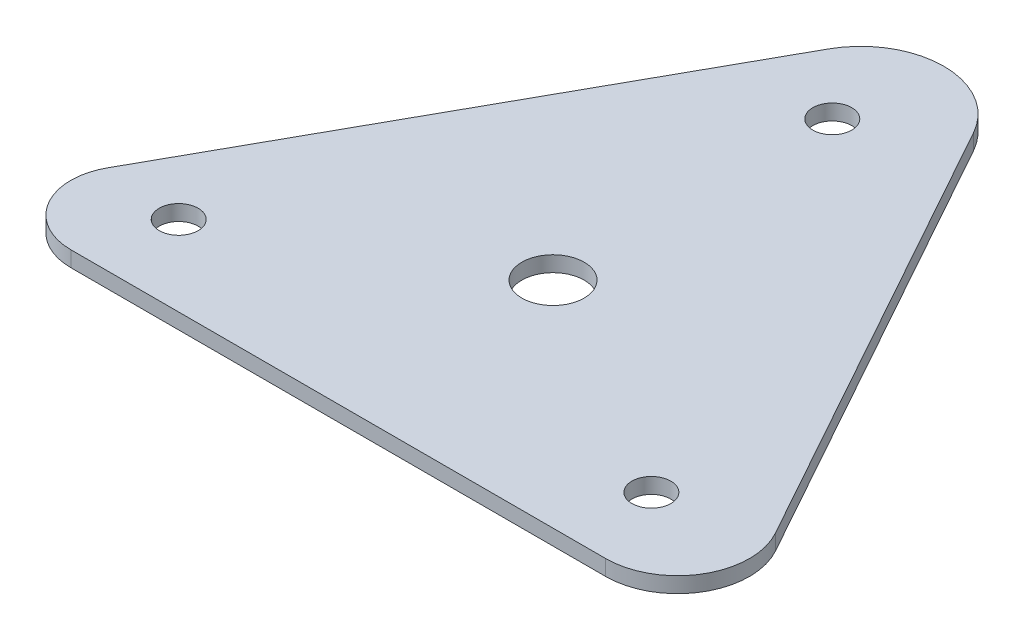
SolidWorks part; units mm, degrees
ref_plane "Front Plane" through (0, 0, 0) normal (0, 0, 1) x (1, 0, 0)
ref_plane "Top Plane" through (0, 0, 0) normal (0, 1, 0) x (1, 0, 0)
ref_plane "Right Plane" through (0, 0, 0) normal (1, 0, 0) x (0, 0, -1)
sketch "Sketch1" plane through (0, 0, 0) normal (0, 1, 0) x (1, 0, 0)
  line L0 (0, 0) -> (109.1184, 0)
  line L1 (121.9408, 21.7924) -> (71.4013, 112.7596)
  line L2 (41.8181, 112.7596) -> (-10.7131, 18.2075)
  line L3 (5.6585, 16.358) -> (54.5592, 100.7792) construction
  line L4 (54.5592, 100.7792) -> (102.0769, 16.358) construction
  line L5 (5.6585, 16.358) -> (102.0769, 16.358) construction
  line L6 (15.5525, 65.4835) -> (43722.9604, -24217.4836) construction
  line L7 (54.5592, 0) -> (54.5592, 50000) construction
  line L8 (96.6711, 67.276) -> (43804.079, 24350.2431) construction
  arc A0 (109.1184, 0) -> (121.9408, 21.7924) centre (109.1184, 14.6685) ccw
  arc A1 (71.4013, 112.7596) -> (41.8181, 112.7596) centre (56.6097, 104.5417) ccw
  arc A2 (-10.7131, 18.2075) -> (0, 0) centre (0, 12.2555) ccw
  circle A3 centre (5.6585, 16.358) radius 3.9688
  circle A4 centre (102.0769, 16.358) radius 3.9687
  circle A5 centre (54.5592, 100.7792) radius 3.9687
  circle A6 centre (54.5592, 43.8122) radius 6.35
  point P10 (56.6097, 121.4628)
  point P14 (-12.2555, 12.2555)
  point P16 (123.7869, 14.6685)
  point P21 (15.5525, 65.4835)
  point P24 (54.5592, 0)
  point P29 (96.6711, 67.276)
  point P30 (54.5592, 43.8122)
  point P31 (54.5592, 43.8122)
  point P32 (54.5592, 43.8122)
  point P33 (54.5592, 43.8122)
  point P34 (54.5592, 43.8122)
  dimension "D2" = 14.6685
  dimension "D4" = 12.7
  dimension "D6" = 12.2555
  dimension "D7" = 121.4628
  dimension "D8" = 7.9375
  dimension "D9" = 7.9375
  dimension "D11" = 97.5614
  dimension "D5" = 7.9375
  dimension "D10" = 96.4184
  dimension "D12" = 96.8756
  dimension "D1" = 109.1184
  dimension "D3" = 104.0638
extrude "Boss-Extrude1" add sketch "Sketch1" along normal blind 3.175
